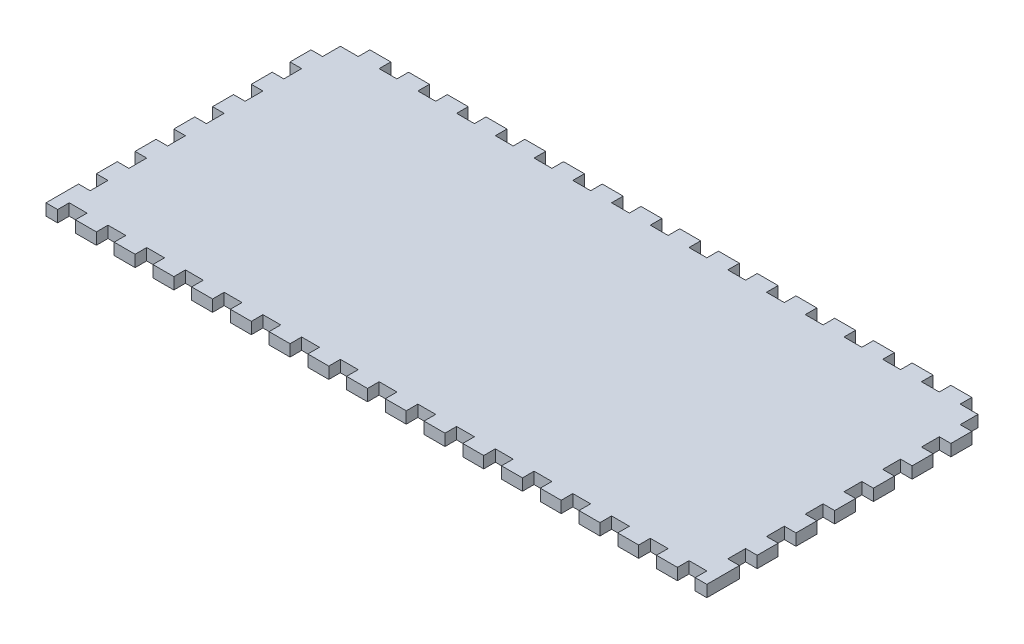
SolidWorks part; units mm, degrees
ref_plane "Спереди" through (0, 0, 0) normal (0, 0, 1) x (1, 0, 0)
ref_plane "Сверху" through (0, 0, 0) normal (0, 1, 0) x (1, 0, 0)
ref_plane "Справа" through (0, 0, 0) normal (1, 0, 0) x (0, 0, -1)
sketch "Эскиз1" plane through (0, 0, 0) normal (0, 1, 0) x (1, 0, 0)
  line L0 (4.6, 70) -> (4.6, 73)
  line L1 (0, 0) -> (4.6, 0)
  line L3 (0, 70) -> (4.6, 70)
  line L5 (4.6, 73) -> (10, 73)
  line L6 (10, 73) -> (10, 70)
  line L7 (82.3, 165) -> (82.3, 0) construction
  line L8 (0, 35) -> (165, 35) construction
  line L9 (14.6, 70) -> (14.6, 73)
  line L10 (14.6, 73) -> (20, 73)
  line L11 (20, 73) -> (20, 70)
  line L12 (24.6, 70) -> (24.6, 73)
  line L13 (24.6, 73) -> (30, 73)
  line L14 (30, 73) -> (30, 70)
  line L15 (34.6, 70) -> (34.6, 73)
  line L16 (34.6, 73) -> (40, 73)
  line L17 (40, 73) -> (40, 70)
  line L18 (44.6, 70) -> (44.6, 73)
  line L19 (44.6, 73) -> (50, 73)
  line L20 (50, 73) -> (50, 70)
  line L21 (54.6, 70) -> (54.6, 73)
  line L22 (54.6, 73) -> (60, 73)
  line L23 (60, 73) -> (60, 70)
  line L24 (64.6, 70) -> (64.6, 73)
  line L25 (64.6, 73) -> (70, 73)
  line L26 (70, 73) -> (70, 70)
  line L27 (74.6, 70) -> (74.6, 73)
  line L28 (74.6, 73) -> (80, 73)
  line L29 (80, 73) -> (80, 70)
  line L30 (84.6, 70) -> (84.6, 73)
  line L31 (84.6, 73) -> (90, 73)
  line L32 (90, 73) -> (90, 70)
  line L33 (94.6, 70) -> (94.6, 73)
  line L34 (94.6, 73) -> (100, 73)
  line L35 (100, 73) -> (100, 70)
  line L36 (104.6, 70) -> (104.6, 73)
  line L37 (104.6, 73) -> (110, 73)
  line L38 (110, 73) -> (110, 70)
  line L39 (114.6, 70) -> (114.6, 73)
  line L40 (114.6, 73) -> (120, 73)
  line L41 (120, 73) -> (120, 70)
  line L42 (124.6, 70) -> (124.6, 73)
  line L43 (124.6, 73) -> (130, 73)
  line L44 (130, 73) -> (130, 70)
  line L45 (134.6, 70) -> (134.6, 73)
  line L46 (134.6, 73) -> (140, 73)
  line L47 (140, 73) -> (140, 70)
  line L48 (144.6, 70) -> (144.6, 73)
  line L49 (144.6, 73) -> (150, 73)
  line L50 (150, 73) -> (150, 70)
  line L51 (154.6, 70) -> (154.6, 73)
  line L52 (154.6, 73) -> (160, 73)
  line L53 (160, 73) -> (160, 70)
  line L54 (160, -3) -> (160, 0)
  line L55 (154.6, -3) -> (160, -3)
  line L56 (154.6, 0) -> (154.6, -3)
  line L57 (150, -3) -> (150, 0)
  line L58 (144.6, -3) -> (150, -3)
  line L59 (144.6, 0) -> (144.6, -3)
  line L60 (140, -3) -> (140, 0)
  line L61 (134.6, -3) -> (140, -3)
  line L62 (134.6, 0) -> (134.6, -3)
  line L63 (130, -3) -> (130, 0)
  line L64 (124.6, -3) -> (130, -3)
  line L65 (124.6, 0) -> (124.6, -3)
  line L66 (120, -3) -> (120, 0)
  line L67 (114.6, -3) -> (120, -3)
  line L68 (114.6, 0) -> (114.6, -3)
  line L69 (110, -3) -> (110, 0)
  line L70 (104.6, -3) -> (110, -3)
  line L71 (104.6, 0) -> (104.6, -3)
  line L72 (100, -3) -> (100, 0)
  line L73 (94.6, -3) -> (100, -3)
  line L74 (94.6, 0) -> (94.6, -3)
  line L75 (90, -3) -> (90, 0)
  line L76 (84.6, -3) -> (90, -3)
  line L77 (84.6, 0) -> (84.6, -3)
  line L78 (80, -3) -> (80, 0)
  line L79 (74.6, -3) -> (80, -3)
  line L80 (74.6, 0) -> (74.6, -3)
  line L81 (70, -3) -> (70, 0)
  line L82 (64.6, -3) -> (70, -3)
  line L83 (64.6, 0) -> (64.6, -3)
  line L84 (60, -3) -> (60, 0)
  line L85 (54.6, -3) -> (60, -3)
  line L86 (54.6, 0) -> (54.6, -3)
  line L87 (50, -3) -> (50, 0)
  line L88 (44.6, -3) -> (50, -3)
  line L89 (44.6, 0) -> (44.6, -3)
  line L90 (40, -3) -> (40, 0)
  line L91 (34.6, -3) -> (40, -3)
  line L92 (34.6, 0) -> (34.6, -3)
  line L93 (30, -3) -> (30, 0)
  line L94 (24.6, -3) -> (30, -3)
  line L95 (24.6, 0) -> (24.6, -3)
  line L96 (20, -3) -> (20, 0)
  line L97 (14.6, -3) -> (20, -3)
  line L98 (14.6, 0) -> (14.6, -3)
  line L99 (10, -3) -> (10, 0)
  line L100 (4.6, -3) -> (10, -3)
  line L101 (4.6, 0) -> (4.6, -3)
  line L102 (0, 65.4) -> (-3, 65.4)
  line L103 (-3, 65.4) -> (-3, 60)
  line L104 (-3, 60) -> (0, 60)
  line L105 (0, 55.4) -> (-3, 55.4)
  line L106 (-3, 55.4) -> (-3, 50)
  line L107 (-3, 50) -> (0, 50)
  line L108 (0, 45.4) -> (-3, 45.4)
  line L109 (-3, 45.4) -> (-3, 40)
  line L110 (-3, 40) -> (0, 40)
  line L111 (0, 35.4) -> (-3, 35.4)
  line L112 (-3, 35.4) -> (-3, 30)
  line L113 (-3, 30) -> (0, 30)
  line L114 (0, 25.4) -> (-3, 25.4)
  line L115 (-3, 25.4) -> (-3, 20)
  line L116 (-3, 20) -> (0, 20)
  line L117 (0, 15.4) -> (-3, 15.4)
  line L118 (-3, 15.4) -> (-3, 10)
  line L119 (-3, 10) -> (0, 10)
  line L120 (0, 5.4) -> (-3, 5.4)
  line L121 (-3, 5.4) -> (-3, -3)
  line L178 (167.6, 5.4) -> (167.6, -3)
  line L179 (164.6, 5.4) -> (167.6, 5.4)
  line L180 (167.6, 10) -> (164.6, 10)
  line L181 (167.6, 15.4) -> (167.6, 10)
  line L182 (164.6, 15.4) -> (167.6, 15.4)
  line L183 (167.6, 20) -> (164.6, 20)
  line L184 (167.6, 25.4) -> (167.6, 20)
  line L185 (164.6, 25.4) -> (167.6, 25.4)
  line L186 (167.6, 30) -> (164.6, 30)
  line L187 (167.6, 35.4) -> (167.6, 30)
  line L188 (164.6, 35.4) -> (167.6, 35.4)
  line L189 (167.6, 40) -> (164.6, 40)
  line L190 (167.6, 45.4) -> (167.6, 40)
  line L191 (164.6, 45.4) -> (167.6, 45.4)
  line L192 (167.6, 50) -> (164.6, 50)
  line L193 (167.6, 55.4) -> (167.6, 50)
  line L194 (164.6, 55.4) -> (167.6, 55.4)
  line L195 (167.6, 60) -> (164.6, 60)
  line L196 (167.6, 65.4) -> (167.6, 60)
  line L197 (164.6, 65.4) -> (167.6, 65.4)
  line L198 (160, 70) -> (164.6, 70)
  line L199 (150, 70) -> (154.6, 70)
  line L200 (140, 70) -> (144.6, 70)
  line L201 (130, 70) -> (134.6, 70)
  line L202 (120, 70) -> (124.6, 70)
  line L203 (110, 70) -> (114.6, 70)
  line L204 (100, 70) -> (104.6, 70)
  line L205 (90, 70) -> (94.6, 70)
  line L206 (80, 70) -> (84.6, 70)
  line L207 (70, 70) -> (74.6, 70)
  line L208 (60, 70) -> (64.6, 70)
  line L209 (164.6, 65.4) -> (164.6, 70)
  line L210 (164.6, 55.4) -> (164.6, 60)
  line L211 (164.6, 45.4) -> (164.6, 50)
  line L212 (164.6, 35.4) -> (164.6, 40)
  line L213 (164.6, 25.4) -> (164.6, 30)
  line L214 (164.6, 15.4) -> (164.6, 20)
  line L215 (164.6, 5.4) -> (164.6, 10)
  line L216 (50, 70) -> (54.6, 70)
  line L217 (40, 70) -> (44.6, 70)
  line L218 (30, 70) -> (34.6, 70)
  line L219 (20, 70) -> (24.6, 70)
  line L220 (10, 70) -> (14.6, 70)
  line L228 (160, 0) -> (164.6, 0)
  line L229 (150, 0) -> (154.6, 0)
  line L230 (140, 0) -> (144.6, 0)
  line L233 (0, 65.4) -> (0, 70)
  line L234 (0, 55.4) -> (0, 60)
  line L235 (0, 45.4) -> (0, 50)
  line L236 (0, 35.4) -> (0, 40)
  line L237 (0, 25.4) -> (0, 30)
  line L238 (0, 15.4) -> (0, 20)
  line L239 (0, 5.4) -> (0, 10)
  line L249 (10, 0) -> (14.6, 0)
  line L250 (20, 0) -> (24.6, 0)
  line L251 (30, 0) -> (34.6, 0)
  line L252 (40, 0) -> (44.6, 0)
  line L253 (50, 0) -> (54.6, 0)
  line L254 (60, 0) -> (64.6, 0)
  line L255 (70, 0) -> (74.6, 0)
  line L256 (80, 0) -> (84.6, 0)
  line L257 (90, 0) -> (94.6, 0)
  line L258 (100, 0) -> (104.6, 0)
  line L259 (110, 0) -> (114.6, 0)
  line L260 (120, 0) -> (124.6, 0)
  line L261 (130, 0) -> (134.6, 0)
  line L262 (167.6, -3) -> (164.6, -3)
  line L263 (-3, -3) -> (0, -3)
  line L264 (0, -3) -> (0, 0)
  line L265 (164.6, -3) -> (164.6, 0)
  line L266 (-3, 0) -> (0, 0) [skipped]
  line L267 (-3, 5.4) -> (-3, 0) [skipped]
  point P12 (7.3, 73)
  point P14 (17.3, 73)
  point P141 (-3, 62.7)
  point P144 (-3, 52.7)
  dimension "D3" = 5.4
  dimension "D4" = 3
  dimension "D5" = 10
  dimension "D6" = 16
  dimension "D7" = 10
  dimension "D8" = 3
  dimension "D9" = 5.4
  dimension "D10" = 10
  dimension "D12" = 10
  dimension "D13" = 10
  dimension "D14" = 8.4
  dimension "D15" = 3
  dimension "D16" = 8.4
  dimension "D17" = 3
  dimension "D18" = 4.6
  dimension "D11" = 7
extrude "Бобышка-Вытянуть1" add sketch "Эскиз1" along normal blind 3
